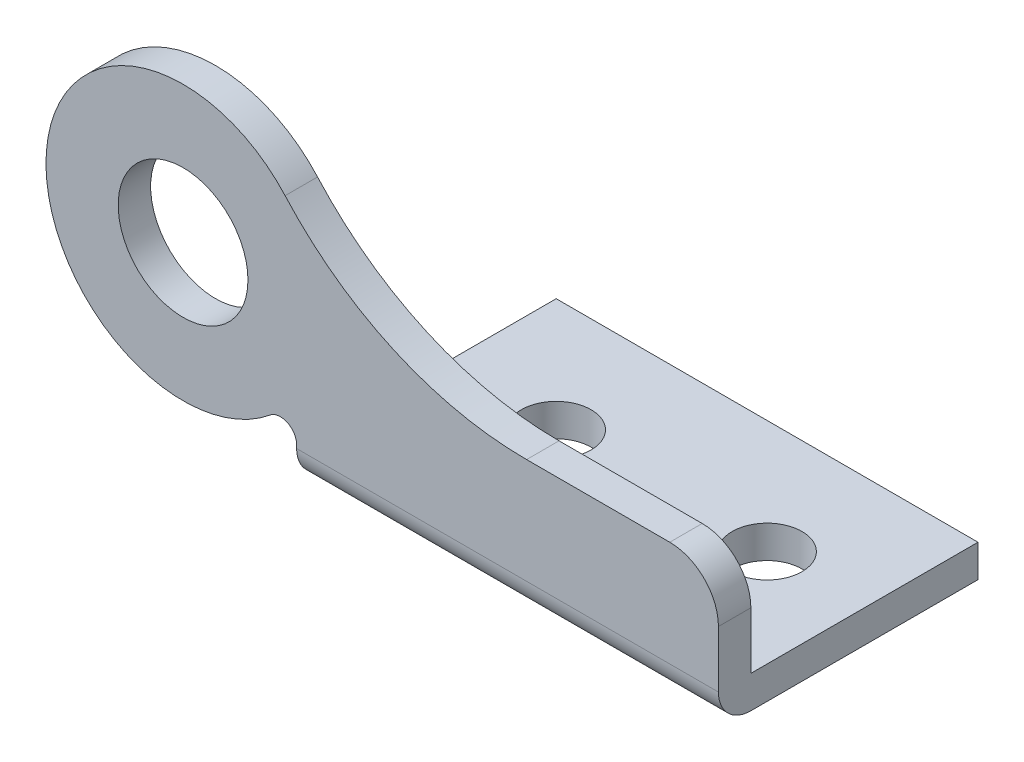
SolidWorks part; units mm, degrees
material "6061 合金"
ref_plane "前视基准面" through (0, 0, 0) normal (0, 0, 1) x (1, 0, 0)
ref_plane "上视基准面" through (0, 0, 0) normal (0, 1, 0) x (1, 0, 0)
ref_plane "右视基准面" through (0, 0, 0) normal (1, 0, 0) x (0, 0, -1)
sketch "草图1" plane through (0, 0, 0) normal (0, 0, 1) x (1, 0, 0)
  line L0 (-4.3582, -7.0519) -> (-4.3582, -7.2511)
  line L1 (-4.3582, -7.2511) -> (21.6418, -7.2511)
  line L2 (21.6418, -7.2511) -> (21.6418, -3.7511)
  line L3 (18.6418, -0.7511) -> (9.8173, -0.7511)
  line L4 (21.6418, -7.2511) -> (21.6418, -9.2511)
  line L5 (19.6418, -9.2511) -> (-2.3582, -9.2511)
  line L6 (-4.3582, -9.2511) -> (-2.3582, -9.2511)
  line L7 (-4.3582, -7.2511) -> (-4.3582, -9.2511)
  line L8 (19.6418, -9.2511) -> (21.6418, -9.2511)
  arc A0 (-4.3582, -7.0519) -> (-5.9932, -6.2793) centre (-5.3582, -7.0519) ccw
  arc A1 (21.6418, -3.7511) -> (18.6418, -0.7511) centre (18.6418, -3.7511) ccw
  arc A2 (-5.0689, 5.8922) -> (9.8173, -0.7511) centre (9.8173, 19.2489) ccw
  arc A3 (-5.0689, 5.8922) -> (-5.9932, -6.2793) centre (-11.3582, 0.2489) ccw
  arc A4 (-11.3582, 4.2489) -> (-11.3582, -3.7511) centre (-11.3582, 0.2489) ccw
  arc A5 (-11.3582, -3.7511) -> (-11.3582, 4.2489) centre (-11.3582, 0.2489) ccw
extrude "凸台-拉伸1" add sketch "草图1" along normal blind 2 contours A2 A3 A0 L0 L1 L2 A1 L3 A5 A4 | L5 L8 L4 L1 L7 L6
sketch "草图2" plane through (0, -9.2511, 0) normal (0, -1, 0) x (1, 0, 0)
  line L0 (19.6418, 16) -> (-2.3582, 16) construction
  line L1 (21.6418, 0) -> (-4.3582, 0) construction
  line L2 (-4.3582, 2) -> (-4.3582, 0) construction
  line L3 (-4.3582, 14) -> (-4.3582, 2) construction
  line L4 (2.6418, 9) -> (15.6418, 9) construction
  line L5 (19.6418, 14) -> (21.6418, 14) construction
  line L6 (19.6418, 14) -> (19.6418, 16) construction
  line L7 (21.6418, 14) -> (21.6418, 0) construction
  line L8 (21.6418, 2) -> (21.6418, 0) construction
  line L9 (21.6418, 0) -> (-4.3582, 0) construction
  line L10 (-4.3582, 2) -> (-4.3582, -14)
  line L11 (-4.3582, -14) -> (21.6418, -14)
  line L12 (21.6418, -14) -> (21.6418, 2)
  line L13 (21.6418, 2) -> (-4.3582, 2) construction
  line L14 (-4.3582, 1) -> (21.6418, 1) construction
  line L15 (2.6418, -7) -> (15.6418, -7) construction
  line L16 (-4.3582, 2) -> (21.6418, 2)
  arc A0 (17.7918, 9) -> (13.8244, 10.1488) centre (15.6418, 9) ccw construction
  arc A1 (13.8244, 10.1488) -> (17.7918, 9) centre (15.6418, 9) ccw construction
  circle A2 centre (2.6418, 9) radius 2.15 construction
  arc A3 (-2.3582, 16) -> (-4.3582, 14) centre (-2.3582, 14) ccw construction
  arc A4 (21.6418, 14) -> (19.6418, 16) centre (19.6418, 14) ccw construction
  circle A5 centre (2.6418, -7) radius 2.15
  arc A6 (13.8244, -8.1488) -> (17.7918, -7) centre (15.6418, -7) cw
  arc A7 (17.7918, -7) -> (13.8244, -8.1488) centre (15.6418, -7) cw
  dimension "D3" = 2.15
  dimension "D4" = 2.15
  dimension "D7" = 2
  dimension "D8" = 2
  dimension "D1" = 26
  dimension "D2" = 7
  dimension "D5" = 7
  dimension "D6" = 16
  dimension "D9" = 13
  dimension "D10" = 16
extrude "凸台-拉伸2" add sketch "草图2" against normal blind 2
fillet "圆角1" radius 2 1 edges at (8.6418, -9.2511, 2)
